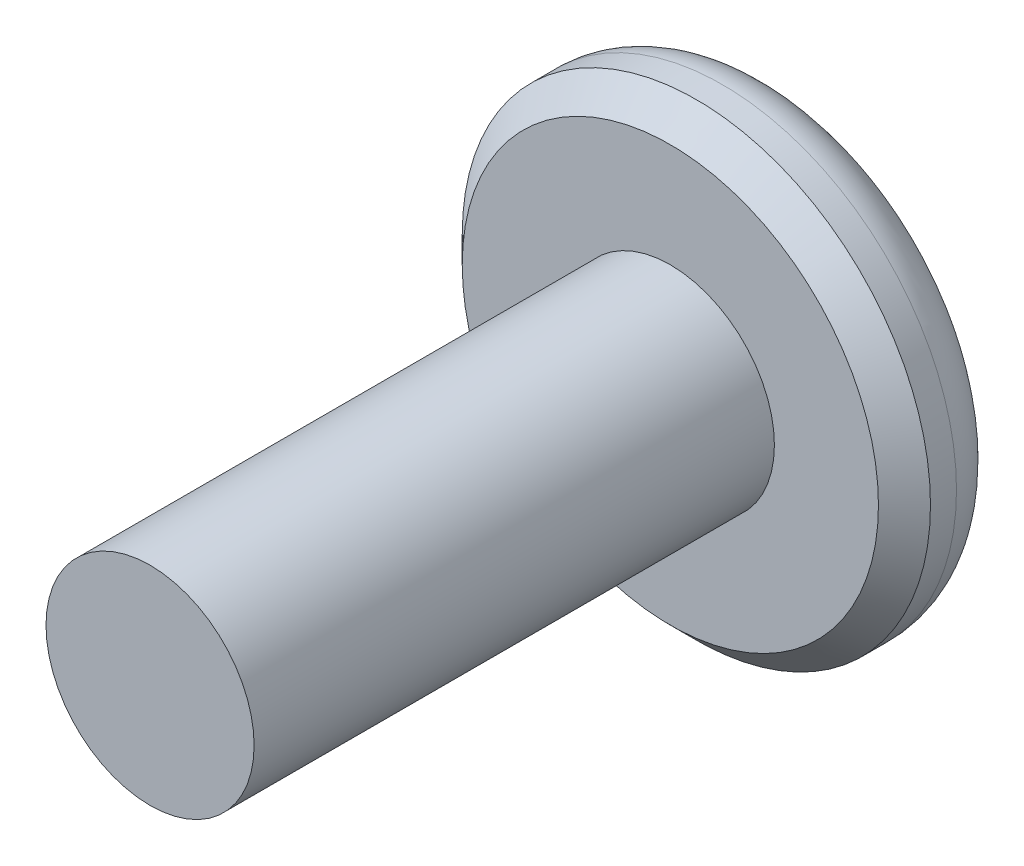
SolidWorks part; units mm, degrees
material "AISI 304"
ref_plane "前视基准面" through (0, 0, 0) normal (0, 0, 1) x (1, 0, 0)
ref_plane "上视基准面" through (0, 0, 0) normal (0, 1, 0) x (1, 0, 0)
ref_plane "右视基准面" through (0, 0, 0) normal (1, 0, 0) x (0, 0, -1)
sketch "草图1" plane through (0, 0, 0) normal (0, 0, 1) x (1, 0, 0)
  circle A0 centre (0, 0) radius 4.5
  dimension "D1" = 9
extrude "凸台-拉伸1" add sketch "草图1" along normal blind 2
sketch "草图2" plane through (0, 0, 2) normal (0, 0, 1) x (1, 0, 0)
  circle A0 centre (0, 0) radius 2
  dimension "D1" = 4
extrude "凸台-拉伸2" add sketch "草图2" along normal blind 10
fillet "圆角1" radius 1 1 edges at (4.5, 0, 0)
chamfer "倒角1" distance 0.5 angle 45 1 edges at (4.5, 0, 2)
sketch "草图3" plane through (0, 0, 0) normal (0, 0, -1) x (-1, 0, 0)
  line L1 (-0.866, 1.5) -> (-1.7321, 0)
  line L2 (-1.7321, 0) -> (-0.866, -1.5)
  line L3 (-0.866, -1.5) -> (0.866, -1.5)
  line L4 (0.866, -1.5) -> (1.7321, 0)
  line L5 (1.7321, 0) -> (0.866, 1.5)
  line L6 (0.866, 1.5) -> (-0.866, 1.5)
  circle A0 centre (0, 0) radius 1.5 construction
  dimension "D1" = 3
extrude "切除-拉伸1" cut sketch "草图3" against normal blind 1
